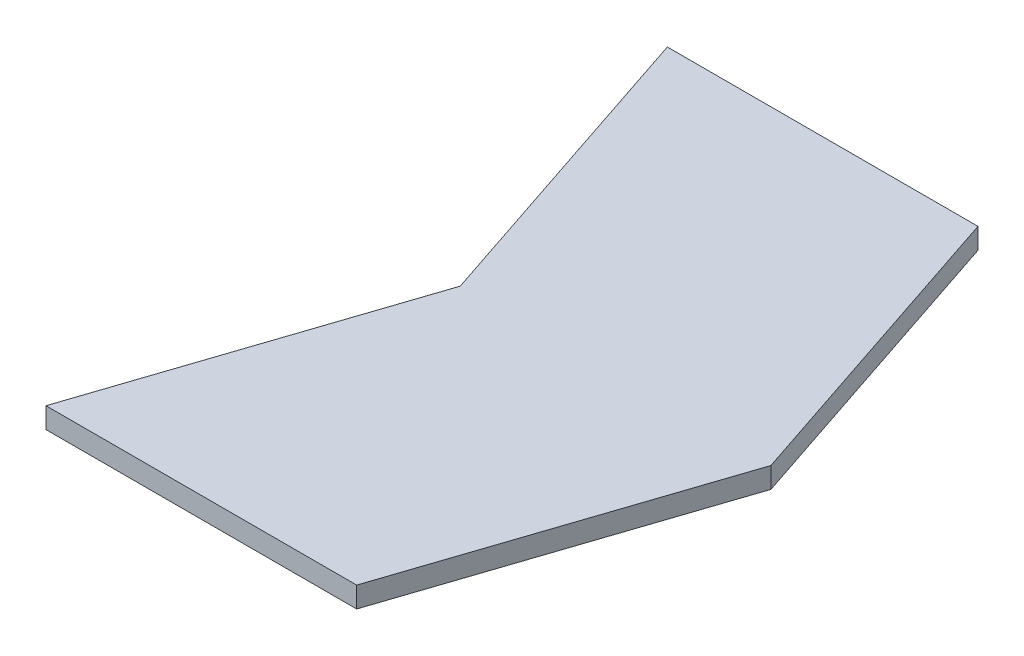
SolidWorks part; units mm, degrees
material "1060 Alloy"
ref_plane "Front Plane" through (0, 0, 0) normal (0, 0, 1) x (1, 0, 0)
ref_plane "Top Plane" through (0, 0, 0) normal (0, 1, 0) x (1, 0, 0)
ref_plane "Right Plane" through (0, 0, 0) normal (1, 0, 0) x (0, 0, -1)
sketch "Sketch1" plane through (0, 0, 0) normal (0, 1, 0) x (1, 0, 0)
  line L0 (0, 0) -> (19.05, 0)
  line L1 (19.05, 0) -> (25.4, 19.05)
  line L2 (25.4, 19.05) -> (19.05, 38.1)
  line L3 (19.05, 38.1) -> (0, 38.1)
  line L4 (0, 38.1) -> (6.35, 19.05)
  line L5 (6.35, 19.05) -> (0, 0)
  dimension "D1" = 19.05
  dimension "D2" = 38.1
  dimension "D3" = 6.35
  dimension "D5" = 19.05
extrude "Boss-Extrude1" add sketch "Sketch1" along normal blind 1.27
